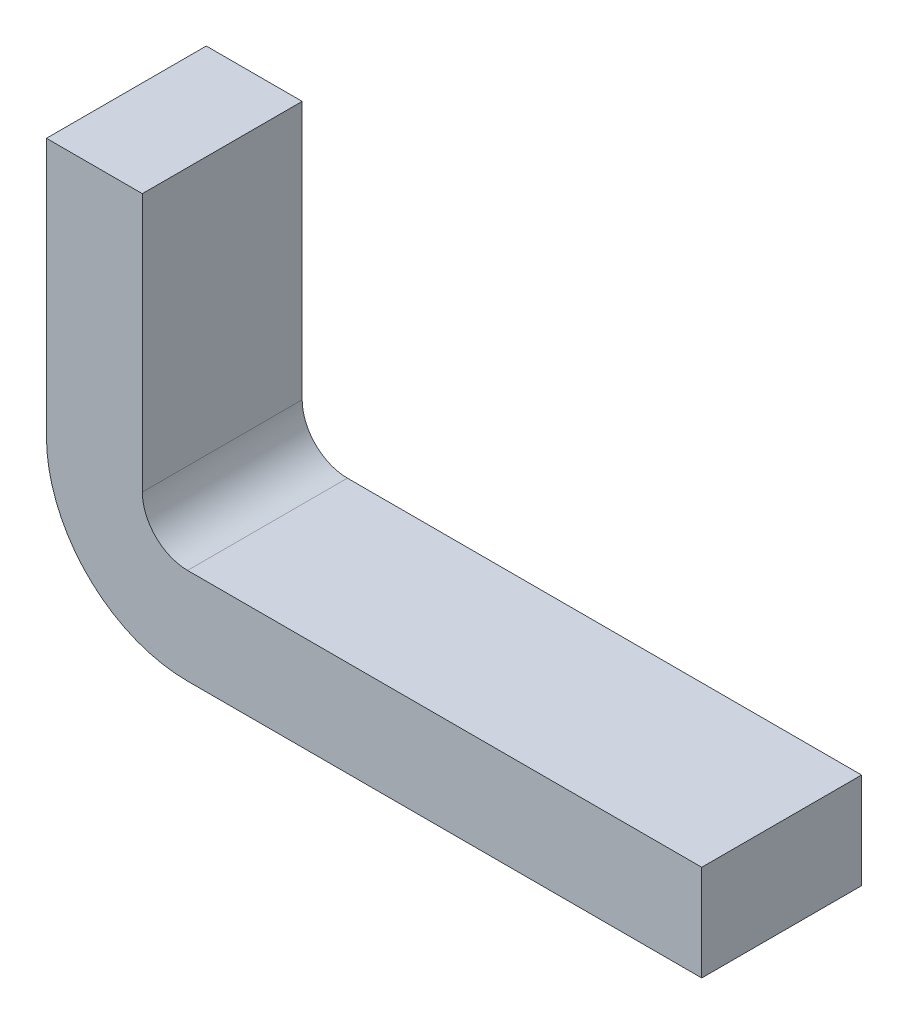
SolidWorks part; units mm, degrees
ref_plane "Alzado" through (0, 0, 0) normal (0, 0, 1) x (1, 0, 0)
ref_plane "Planta" through (0, 0, 0) normal (0, 1, 0) x (1, 0, 0)
ref_plane "Vista lateral" through (0, 0, 0) normal (1, 0, 0) x (0, 0, -1)
sketch "Croquis1" plane through (0, 0, 0) normal (0, 0, 1) x (1, 0, 0)
  line L6 (1.9, 0.15) -> (0.2915, 0.15) construction
  line L7 (0, 0.4415) -> (0, 1.25) construction
  line L8 (1.9, 0.3) -> (0.2915, 0.3)
  line L9 (0.15, 0.4415) -> (0.15, 1.25)
  line L10 (1.9, 0) -> (0.2915, 0)
  line L11 (-0.15, 0.4415) -> (-0.15, 1.25)
  line L12 (1.9, 0.3) -> (1.9, 0)
  line L13 (0.15, 1.25) -> (-0.15, 1.25)
  line L14 (-200003.7753, 0.3) -> (200002.2056, 0.3) construction
  line L15 (-200003.3054, 1.25) -> (200002.6754, 1.25) construction
  line L16 (0, 0.4415) -> (0, 1.25) construction
  line L17 (0.2915, 0.3) -> (0.2915, 0) construction
  arc A2 (0.2915, 0.15) -> (0, 0.4415) centre (0.2915, 0.4415) cw construction
  arc A3 (0.2915, 0.3) -> (0.15, 0.4415) centre (0.2915, 0.4415) cw
  arc A4 (0.2915, 0) -> (-0.15, 0.4415) centre (0.2915, 0.4415) cw
  arc A5 (0.2915, 0.15) -> (0, 0.4415) centre (0.2915, 0.4415) cw construction
  point P1 (0, 0)
  point P2 (0, 0)
  point P3 (2.927, 0)
  point P4 (3.6887, 0)
  point P7 (0, 0)
  point P20 (0, 0)
  point P21 (0.15, 1.5207)
  point P22 (0, 0)
  point P23 (2.9119, 0.3)
  point P25 (0, 0)
  point P26 (0.7142, 0.8838)
  point P27 (0, 0)
  point P28 (0, 0)
  point P29 (0, 0)
  point P30 (0, 0)
  point P33 (0.15, 1.1069)
  point P35 (0, 0)
  point P36 (0, 0)
  point P37 (0.15, 1.178)
  point P38 (0, 0)
  point P39 (0, 0)
extrude "Saliente-Extruir1" add sketch "Croquis1" along normal up to vertex (0.25 mm away) and the other way up to vertex (0.25 mm away)
